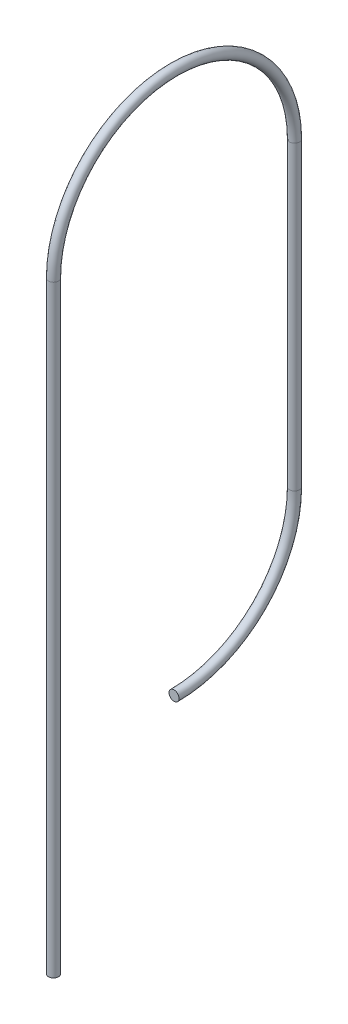
SolidWorks part; units mm, degrees
ref_plane "Front Plane" through (0, 0, 0) normal (0, 0, 1) x (1, 0, 0)
ref_plane "Top Plane" through (0, 0, 0) normal (0, 1, 0) x (1, 0, 0)
ref_plane "Right Plane" through (0, 0, 0) normal (1, 0, 0) x (0, 0, -1)
sketch "Sketch3" plane through (0, 0, 0) normal (1, 0, 0) x (0, 0, -1)
  line L0 (0, 0) -> (0, 150)
  line L1 (0, 55) -> (0, -55) construction
  line L2 (60, 150) -> (60, 75)
  arc A0 (0, 150) -> (60, 150) centre (30, 150) cw
  arc A1 (60, 75) -> (30.0065, 45) centre (30, 75) cw
  dimension "D1" = 30
  dimension "D4" = 30
  dimension "D2" = 150
  dimension "D3" = 75
sketch "Sketch4" plane through (0, 0, 0) normal (0, 1, 0) x (1, 0, 0)
  circle A0 centre (0, 0) radius 1.25
  dimension "D1" = 2.5
sweep "Sweep2" add profiles "Sketch4" path "Sketch3"
